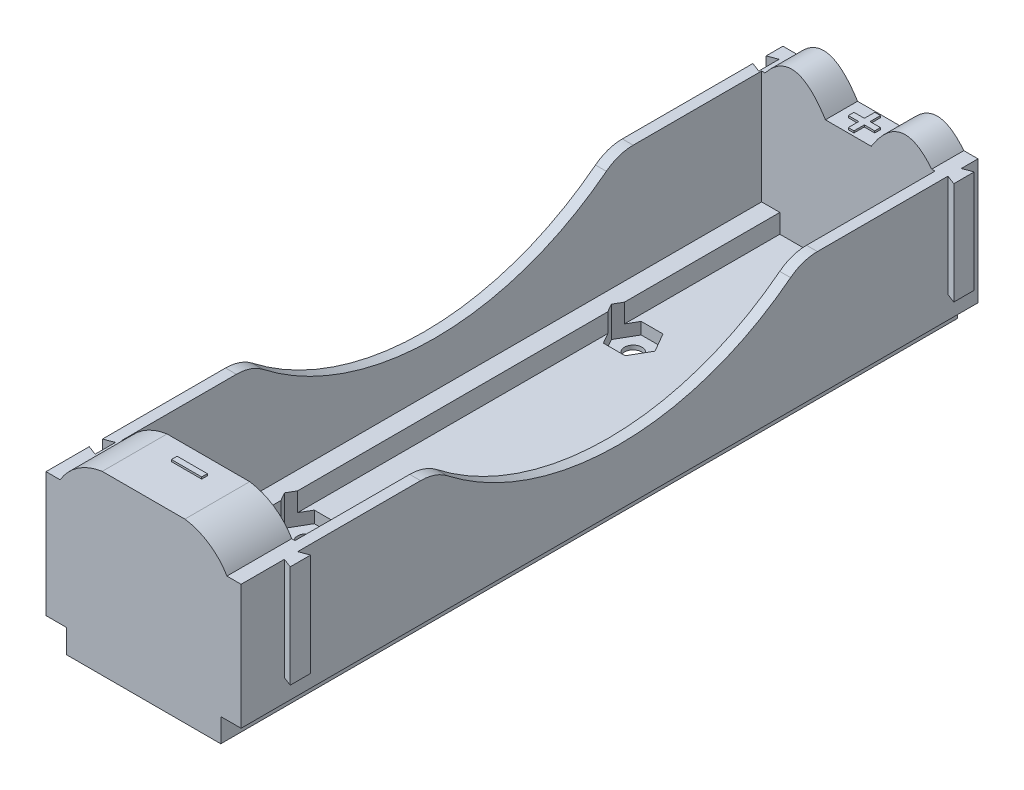
SolidWorks part; units mm, degrees
material "PP Copolymer"
ref_plane "Front Plane" through (0, 0, 0) normal (0, 0, 1) x (1, 0, 0)
ref_plane "Top Plane" through (0, 0, 0) normal (0, 1, 0) x (1, 0, 0)
ref_plane "Right Plane" through (0, 0, 0) normal (1, 0, 0) x (0, 0, -1)
sketch "Sketch1" plane through (0, 0, 0) normal (0, 0, 1) x (1, 0, 0)
  line L0 (0, 0) -> (0, 50000) construction
  line L1 (0, 0) -> (50000, 0) construction
  line L2 (8.175, 0) -> (-8.175, 0)
  line L3 (-8.175, 0) -> (-8.175, 2.5)
  line L4 (-8.175, 2.5) -> (-10.325, 2.5)
  line L5 (-10.325, 2.5) -> (-10.325, 15.7)
  line L6 (-10.325, 15.7) -> (10.325, 15.7)
  line L9 (10.325, 2.5) -> (10.325, 15.7)
  line L10 (8.175, 2.5) -> (10.325, 2.5)
  line L11 (8.175, 0) -> (8.175, 2.5)
  point P21 (0, 0)
  dimension "D1" = 13.2
  dimension "D2" = 20.65
  dimension "D3" = 2.15
  dimension "D4" = 2.5
extrude "Extrude1" add sketch "Sketch1" against normal blind 40
sketch "Sketch2" plane through (0, 0, 0) normal (0, 0, 1) x (1, 0, 0)
  line L0 (0, 0) -> (0, 50000) construction
  line L1 (-8.175, 0) -> (8.175, 0) construction
  line L2 (10.325, 15.7) -> (-10.325, 15.7) construction
  line L3 (-8.825, 15.7) -> (8.825, 15.7)
  line L4 (-4.375, 18.7) -> (4.375, 18.7)
  line L5 (-10.325, 15.7) -> (-10.325, 2.5) construction
  arc A0 (-8.825, 15.7) -> (-4.375, 18.7) centre (-3.5, 12.6017) cw
  arc A1 (8.825, 15.7) -> (4.375, 18.7) centre (3.5, 12.6017) ccw
  point P4 (0, 0)
  point P12 (0, 15.7)
  dimension "D4" = 3.5
  dimension "D1" = 8.75
  dimension "D2" = 1.5
  dimension "D3" = 18.7
extrude "Extrude2" add sketch "Sketch2" against normal blind 6.86
sketch "Sketch4" plane through (0, 0, -40) normal (0, 0, -1) x (-1, 0, 0)
  line L0 (0, 0) -> (0, 50000) construction
  line L1 (8.175, 0) -> (-8.175, 0) construction
  line L2 (-10.325, 15.7) -> (-8.825, 15.7)
  line L3 (8.825, 15.7) -> (-8.825, 15.7) construction
  line L4 (2.425, 14.6) -> (-2.425, 14.6)
  line L5 (-12.212, 17.46) -> (49987.788, 17.46) construction
  line L6 (10.325, 15.7) -> (8.825, 15.7)
  line L7 (-10.325, 15.7) -> (10.325, 15.7) construction
  line L8 (-6.0115, 17.46) -> (-6.0115, 16.3356) construction
  line L9 (10.325, 15.7) -> (10.325, 2.5) construction
  line L10 (10.325, 2.5) -> (8.175, 2.5) construction
  line L11 (8.175, 2.5) -> (8.175, 0) construction
  line L12 (-8.175, 0) -> (-8.175, 2.5) construction
  line L13 (-8.175, 2.5) -> (-10.325, 2.5) construction
  line L14 (-10.325, 2.5) -> (-10.325, 15.7) construction
  line L15 (10.325, 15.7) -> (10.325, 2.5)
  line L16 (10.325, 2.5) -> (8.175, 2.5)
  line L17 (8.175, 2.5) -> (8.175, 0)
  line L18 (8.175, 0) -> (-8.175, 0)
  line L19 (-8.175, 0) -> (-8.175, 2.5)
  line L20 (-8.175, 2.5) -> (-10.325, 2.5)
  line L21 (-10.325, 2.5) -> (-10.325, 15.7)
  parabola Q0 (-2.425, 14.6) -> (-8.825, 15.7) focus (-6.0115, 16.3356) apex (-6.0115, 17.46)
  parabola Q1 (2.425, 14.6) -> (8.825, 15.7) focus (6.0115, 16.3356) apex (6.0115, 17.46)
  point P4 (0, 0)
  point P19 (0, 14.6)
  dimension "D1" = 17.46
  dimension "D2" = 14.6
  dimension "D3" = 4.85
  dimension "D4" = 1.5
extrude "Extrude3" add sketch "Sketch4" along normal offset from surface (38 mm away) 78 up to face at (0.4958, 9.1833, 0)
sketch "Sketch5" plane through (0, 15.7, 0) normal (0, 1, 0) x (1, 0, 0)
  line L0 (0, 0) -> (0, 50000) construction
  line L1 (10.325, 78) -> (10.325, 0) construction
  line L2 (-9.175, 74.6) -> (9.175, 74.6)
  line L3 (-9.175, 74.6) -> (-9.175, 6.86)
  line L4 (-9.175, 6.86) -> (9.175, 6.86)
  line L5 (9.175, 74.6) -> (9.175, 6.86)
  line L6 (-9.175, 74.6) -> (9.175, 6.86) construction
  line L7 (-9.175, 6.86) -> (9.175, 74.6) construction
  line L8 (10.325, 0) -> (8.825, 0) construction
  line L9 (2.425, 78) -> (-2.425, 78) construction
  point P3 (0, 40.73)
  dimension "D1" = 1.15
  dimension "D2" = 6.86
  dimension "D3" = 3.4
extrude "Extrude4" cut sketch "Sketch5" against normal blind 12 and the other way through all
sketch "Sketch6" plane through (0, 3.7, 0) normal (0, 1, 0) x (1, 0, 0)
  line L0 (0, 0) -> (0, 50000) construction
  line L1 (4.375, 0) -> (-4.375, 0) construction
  line L2 (2.425, 74.6) -> (-2.425, 74.6) construction
  line L3 (-7.25, 74.6) -> (7.25, 74.6)
  line L4 (-7.25, 74.6) -> (-7.25, 6.86)
  line L5 (-7.25, 6.86) -> (7.25, 6.86)
  line L6 (7.25, 74.6) -> (7.25, 6.86)
  line L7 (-7.25, 74.6) -> (7.25, 6.86) construction
  line L8 (-7.25, 6.86) -> (7.25, 74.6) construction
  line L9 (4.375, 6.86) -> (-4.375, 6.86) construction
  point P4 (0, 0)
  point P5 (0, 40.73)
  dimension "D1" = 14.5
extrude "Extrude5" cut sketch "Sketch6" against normal offset from surface (2 mm away) 14 up to face at (-9.1938, 15.7, -40.5063)
sketch "Sketch7" plane through (10.325, 0, 0) normal (1, 0, 0) x (0, 0, -1)
  line L0 (12.0663, 15.7) -> (19, 15.7)
  line L1 (78, 15.7) -> (0, 15.7) construction
  line L2 (61, 15.7) -> (67.9337, 15.7)
  line L3 (21.8378, 14.727) -> (58.1622, 14.727) construction
  line L4 (11.4454, 8.5) -> (50011.4454, 8.5) construction
  line L5 (78, 0) -> (0, 0) construction
  line L6 (19, 15.7) -> (21.8378, 14.727) construction
  line L7 (0, 2.5) -> (0, 15.7) construction
  line L8 (12.0663, 15.7) -> (12.0663, 19.9911)
  line L9 (12.0663, 19.9911) -> (67.9337, 19.9911)
  line L10 (67.9337, 19.9911) -> (67.9337, 15.7)
  arc A0 (21.8378, 14.727) -> (58.1622, 14.727) centre (40, 38.1) ccw
  arc A1 (21.8378, 14.727) -> (19, 15.7) centre (19, 11.075) ccw
  arc A2 (58.1622, 14.727) -> (61, 15.7) centre (61, 11.075) cw
  dimension "D1" = 3
  dimension "D2" = 42
  dimension "D3" = 8.5
  dimension "D4" = 19
extrude "Extrude6" cut sketch "Sketch7" against normal through all
sketch "Sketch8" plane through (0, 15.7, 0) normal (0, 1, 0) x (1, 0, 0)
  line L0 (10.325, 76.22) -> (11.325, 76.6)
  line L1 (10.325, 78) -> (10.325, 61) construction
  line L2 (11.325, 76.6) -> (11.325, 74.44)
  line L3 (10.325, 74.82) -> (11.325, 74.44)
  line L4 (10.325, 74.82) -> (10.325, 76.22)
  line L5 (10.325, 76.22) -> (10.325, 74.82)
  line L6 (10.325, 75.52) -> (11.325, 75.52) construction
  line L7 (10.325, 78) -> (8.825, 78) construction
  line L8 (10.325, 5.98) -> (11.325, 6.36)
  line L9 (10.325, 19) -> (10.325, 0) construction
  line L10 (11.325, 6.36) -> (11.325, 4.2)
  line L11 (11.325, 4.2) -> (10.325, 4.58)
  line L12 (10.325, 4.58) -> (10.325, 5.98)
  line L13 (10.325, 5.28) -> (11.325, 5.28) construction
  line L14 (10.325, 0) -> (8.825, 0) construction
  line M3 (10.325, 61) -> (10.325, 78)
  dimension "D1" = 1.4
  dimension "D2" = 2.16
  dimension "D3" = 1
  dimension "D4" = 1.4
  dimension "D5" = 4.2
extrude "Extrude7" add sketch "Sketch8" against normal blind 10.85 contours L12 L11 L10 L8 | L3 L2 L0 M3
sketch "Sketch9" plane through (0, 15.7, 0) normal (0, 1, 0) x (1, 0, 0)
  line L0 (-10.325, 76.22) -> (-9.325, 76.6)
  line L1 (-10.325, 78) -> (-10.325, 61) construction
  line L2 (-9.325, 76.6) -> (-9.325, 74.44)
  line L3 (-9.325, 74.44) -> (-10.325, 74.82)
  line L4 (-10.325, 74.82) -> (-10.325, 76.22)
  line L5 (10.325, 76.22) -> (11.325, 76.6) construction
  line L6 (11.325, 76.6) -> (11.325, 74.44) construction
  line L7 (10.325, 76.22) -> (10.325, 74.82) construction
  line L8 (-10.325, 75.52) -> (-9.325, 75.52) construction
  line L10 (-9.325, 76.6) -> (11.325, 76.6) construction
  line L11 (-10.325, 5.98) -> (-9.325, 6.36)
  line L12 (-10.325, 19) -> (-10.325, 0) construction
  line L13 (-9.325, 6.36) -> (-9.325, 4.2)
  line L14 (-9.325, 4.2) -> (-10.325, 4.58)
  line L15 (-10.325, 4.58) -> (-10.325, 5.98)
  line L16 (10.325, 5.98) -> (11.325, 6.36) construction
  line L17 (11.325, 6.36) -> (11.325, 4.2) construction
  line L18 (10.325, 5.98) -> (10.325, 4.58) construction
  line L19 (-10.325, 5.28) -> (-9.325, 5.28) construction
  line L20 (-9.325, 6.36) -> (11.325, 6.36) construction
extrude "Extrude8" cut sketch "Sketch9" against normal blind 10.85
sketch "Sketch10" plane through (0, 0, 0) normal (0, -1, 0) x (1, 0, 0)
  line L0 (0, 0) -> (0, -50000) construction
  line L1 (-5.45, -15.1521) -> (-5.45, -50015.1521) construction
  line L2 (-15.3904, -21.75) -> (49984.6096, -21.75) construction
  line L3 (-8.175, 0) -> (8.175, 0) construction
  line L4 (-6.375, -18.47) -> (-6.375, -50018.47) construction
  line L5 (6.375, -17.2311) -> (6.375, -50017.2311) construction
  line L6 (-18.7529, -58.2) -> (49981.2471, -58.2) construction
  circle A0 centre (-5.45, -22.675) radius 0.925
  circle A1 centre (-5.45, -57.275) radius 0.925
  circle A2 centre (5.45, -57.275) radius 0.925
  circle A3 centre (5.45, -22.675) radius 0.925
  dimension "D1" = 1.85
  dimension "D2" = 21.75
  dimension "D3" = 12.75
  dimension "D4" = 36.45
extrude "Extrude9" cut sketch "Sketch10" against normal through all
sketch "Sketch11" plane through (0, 1.7, 0) normal (0, 1, 0) x (1, 0, 0)
  line L1 (-3.1406, 57.275) -> (-4.2953, 59.275)
  line L2 (-4.2953, 59.275) -> (-6.6047, 59.275)
  line L3 (-6.6047, 59.275) -> (-7.7594, 57.275)
  line L4 (-7.7594, 57.275) -> (-6.6047, 55.275)
  line L5 (-6.6047, 55.275) -> (-4.2953, 55.275)
  line L6 (-4.2953, 55.275) -> (-3.1406, 57.275)
  line L7 (3.1406, 57.275) -> (4.2953, 55.275)
  line L8 (4.2953, 55.275) -> (6.6047, 55.275)
  line L9 (6.6047, 55.275) -> (7.7594, 57.275)
  line L10 (7.7594, 57.275) -> (6.6047, 59.275)
  line L11 (6.6047, 59.275) -> (4.2953, 59.275)
  line L12 (4.2953, 59.275) -> (3.1406, 57.275)
  line L13 (-3.1406, 22.675) -> (-4.2953, 24.675)
  line L14 (-4.2953, 24.675) -> (-6.6047, 24.675)
  line L15 (-6.6047, 24.675) -> (-7.7594, 22.675)
  line L16 (-7.7594, 22.675) -> (-6.6047, 20.675)
  line L17 (-6.6047, 20.675) -> (-4.2953, 20.675)
  line L18 (-4.2953, 20.675) -> (-3.1406, 22.675)
  line L19 (3.1406, 22.675) -> (4.2953, 20.675)
  line L20 (4.2953, 20.675) -> (6.6047, 20.675)
  line L21 (6.6047, 20.675) -> (7.7594, 22.675)
  line L22 (7.7594, 22.675) -> (6.6047, 24.675)
  line L23 (6.6047, 24.675) -> (4.2953, 24.675)
  line L24 (4.2953, 24.675) -> (3.1406, 22.675)
  circle A0 centre (-5.45, 57.275) radius 2 construction
  circle A1 centre (5.45, 57.275) radius 2 construction
  circle A2 centre (-5.45, 22.675) radius 2 construction
  circle A3 centre (5.45, 22.675) radius 2 construction
  dimension "D1" = 4
extrude "Extrude10" cut sketch "Sketch11" against normal blind 1.25 and the other way through all
sketch "Sketch12" plane through (0, 18.7, 0) normal (0, 1, 0) x (1, 0, 0)
  line L0 (0, 0) -> (0, 4.8536) construction
  line L1 (-1.6, 5.1536) -> (1.6, 5.1536)
  line L2 (-1.6, 5.1536) -> (-1.6, 4.5536)
  line L3 (-1.6, 4.5536) -> (1.6, 4.5536)
  line L4 (1.6, 5.1536) -> (1.6, 4.5536)
  line L5 (-1.6, 5.1536) -> (1.6, 4.5536) construction
  line L6 (-1.6, 4.5536) -> (1.6, 5.1536) construction
  line L7 (4.375, 0) -> (-4.375, 0) construction
  point P0 (0, 4.8536)
  dimension "D1" = 0.6
  dimension "D2" = 3.2
extrude "Extrude11" add sketch "Sketch12" along normal blind 0.2
sketch "Sketch13" plane through (0, 14.6, 0) normal (0, 1, 0) x (1, 0, 0)
  line L0 (-0.3, 77.7) -> (0.3, 77.7)
  line L1 (0.3, 77.7) -> (0.2958, 76.6)
  line L2 (0.2958, 76.6) -> (1.3958, 76.6)
  line L3 (1.3958, 76.6) -> (1.3958, 76)
  line L4 (1.3958, 76) -> (0.2958, 76)
  line L5 (0.2958, 76) -> (0.2915, 74.9)
  line L6 (0.2915, 74.9) -> (-0.3085, 74.9)
  line L7 (-0.3085, 74.9) -> (-0.3042, 76)
  line L8 (-0.3042, 76) -> (-1.4043, 76)
  line L9 (-1.4043, 76) -> (-1.4043, 76.6)
  line L10 (-1.4043, 76.6) -> (-0.3042, 76.6)
  line L11 (-0.3042, 76.6) -> (-0.3, 77.7)
  line L12 (0, 78) -> (0, 77.7) construction
  line L13 (2.425, 78) -> (-2.425, 78) construction
  line L14 (2.425, 74.6) -> (-2.425, 74.6) construction
  dimension "D1" = 0.6
  dimension "D2" = 0.3
  dimension "D3" = 0.3
extrude "Extrude12" add sketch "Sketch13" along normal blind 0.2
ref_plane "battery top" through (0, 20, 0) normal (0, -1, 0) x (1, 0, 0)
